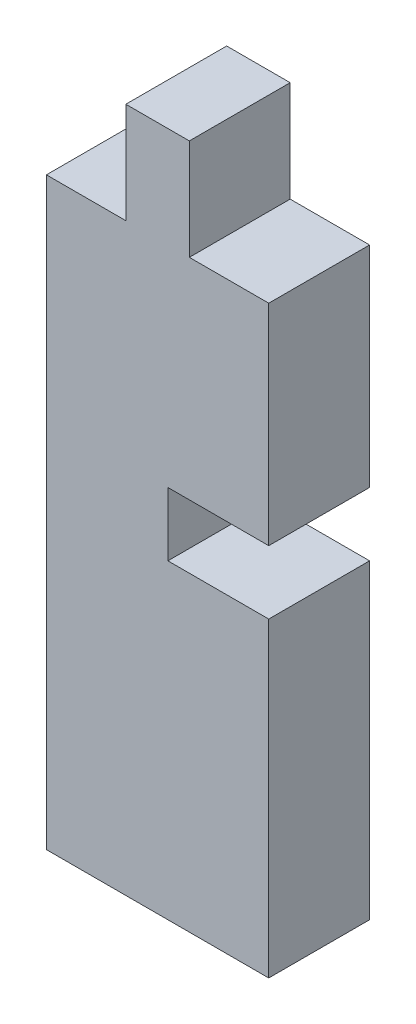
SolidWorks part; units mm, degrees
material "Acrylic (Medium-high impact)"
ref_plane "Front Plane" through (0, 0, 0) normal (0, 0, 1) x (1, 0, 0)
ref_plane "Top Plane" through (0, 0, 0) normal (0, 1, 0) x (1, 0, 0)
ref_plane "Right Plane" through (0, 0, 0) normal (1, 0, 0) x (0, 0, -1)
sketch "Sketch1" plane through (0, 0, 0) normal (0, 0, 1) x (1, 0, 0)
  line L1 (3.5, -10.7875) -> (-3.5, -10.7875)
  line L2 (3.5, -10.7875) -> (3.5, 10.7875)
  line L3 (3.5, 10.7875) -> (-3.5, 10.7875)
  line L4 (-3.5, -10.7875) -> (-3.5, 10.7875)
  line L5 (3.5, -10.7875) -> (-3.5, 10.7875) construction
  line L6 (3.5, 10.7875) -> (-3.5, -10.7875) construction
  line L7 (-1, 10.7875) -> (1, 10.7875)
  line L8 (-1, 10.7875) -> (-1, 7.6125)
  line L9 (-1, 7.6125) -> (1, 7.6125)
  line L10 (1, 10.7875) -> (1, 7.6125)
  line L11 (-3.5, 10.7875) -> (3.5, 10.7875)
  line L12 (-3.5, 10.7875) -> (-3.5, 7.6125)
  line L13 (-3.5, 7.6125) -> (3.5, 7.6125)
  line L14 (3.5, 10.7875) -> (3.5, 7.6125)
  line L15 (3.5, 1) -> (0.325, 1)
  line L16 (3.5, 1) -> (3.5, -1)
  line L17 (3.5, -1) -> (0.325, -1)
  line L18 (0.325, 1) -> (0.325, -1)
  point P0 (0, 0)
  point P14 (0, 7.6125)
  point P15 (0, 7.6125)
  point P18 (0.325, 0)
  dimension "D1" = 7
  dimension "D3" = 2
  dimension "D5" = 3.175
  dimension "D6" = 2
  dimension "D4" = 3.175
  dimension "D2" = 18.4
extrude "Boss-Extrude1" add sketch "Sketch1" along normal blind 3.175 contours L13 L4 L1 L2 L9 | L10 L3 L8 L9
equation "\"bottomThickness\"= .25in"
equation "\"wallThickness\"= .125in"
equation "\"D5@Sketch1\"=\"wallThickness\""
equation "\"D1@Boss-Extrude1\"=\"wallThickness\""
equation "\"D4@Sketch1\"=\"wallThickness\""
